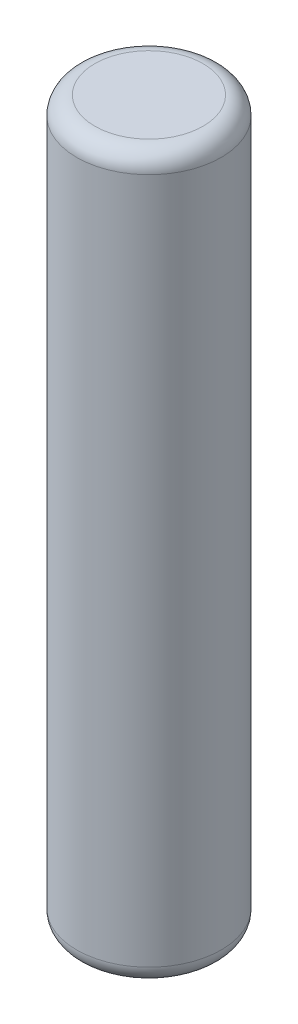
SolidWorks part; units mm, degrees
ref_plane "Front Plane" through (0, 0, 0) normal (0, 0, 1) x (1, 0, 0)
ref_plane "Top Plane" through (0, 0, 0) normal (0, 1, 0) x (1, 0, 0)
ref_plane "Right Plane" through (0, 0, 0) normal (1, 0, 0) x (0, 0, -1)
sketch "Sketch1" plane through (0, 0, 0) normal (0, 1, 0) x (1, 0, 0)
  circle A0 centre (0, 0) radius 4
  dimension "D1" = 8
extrude "Boss-Extrude1" add sketch "Sketch1" along normal blind 40
fillet "Fillet1" radius 1 2 edges at (0, 0, 4) (0, 40, 4)
